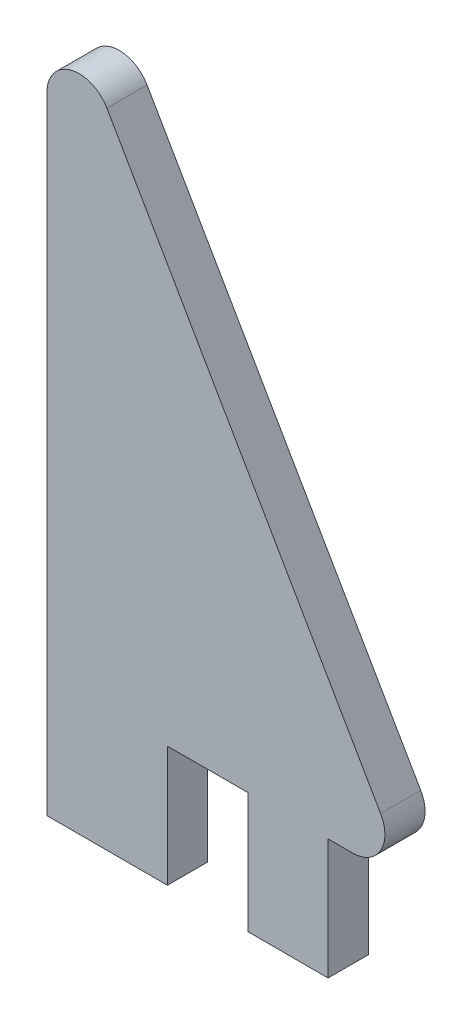
SolidWorks part; units mm, degrees
ref_plane "Front Plane" through (0, 0, 0) normal (0, 0, 1) x (1, 0, 0)
ref_plane "Top Plane" through (0, 0, 0) normal (0, 1, 0) x (1, 0, 0)
ref_plane "Right Plane" through (0, 0, 0) normal (1, 0, 0) x (0, 0, -1)
sketch "Sketch1" plane through (0, 0, 0) normal (0, 0, 1) x (1, 0, 0)
  line L0 (0, 0) -> (0, 49.4934)
  line L1 (0, 49.4934) -> (28.575, 0)
  line L2 (28.575, 0) -> (0, 0)
  line L4 (0, 0) -> (9.525, 0)
  line L5 (0, 0) -> (0, -9.525)
  line L6 (0, -9.525) -> (9.525, -9.525)
  line L7 (9.525, 0) -> (9.525, -9.525)
  line L8 (15.875, 0) -> (22.225, 0)
  line L9 (15.875, 0) -> (15.875, -9.525)
  line L10 (15.875, -9.525) -> (22.225, -9.525)
  line L11 (22.225, 0) -> (22.225, -9.525)
  point P11 (9.525, -4.7625)
  dimension "D1" = 28.575
  dimension "D2" = 60
  dimension "D3" = 9.525
  dimension "D4" = 9.525
  dimension "D5" = 6.35
  dimension "D6" = 6.35
extrude "Boss-Extrude1" add sketch "Sketch1" along normal blind 3.175 contours L2 L1 L0 | L7 L2 L5 L6 | L11 L2 L9 L10
fillet "Fillet1" radius 2.54 2 edges at (28.575, 0, 1.5875) (0, 49.4934, 1.5875)
